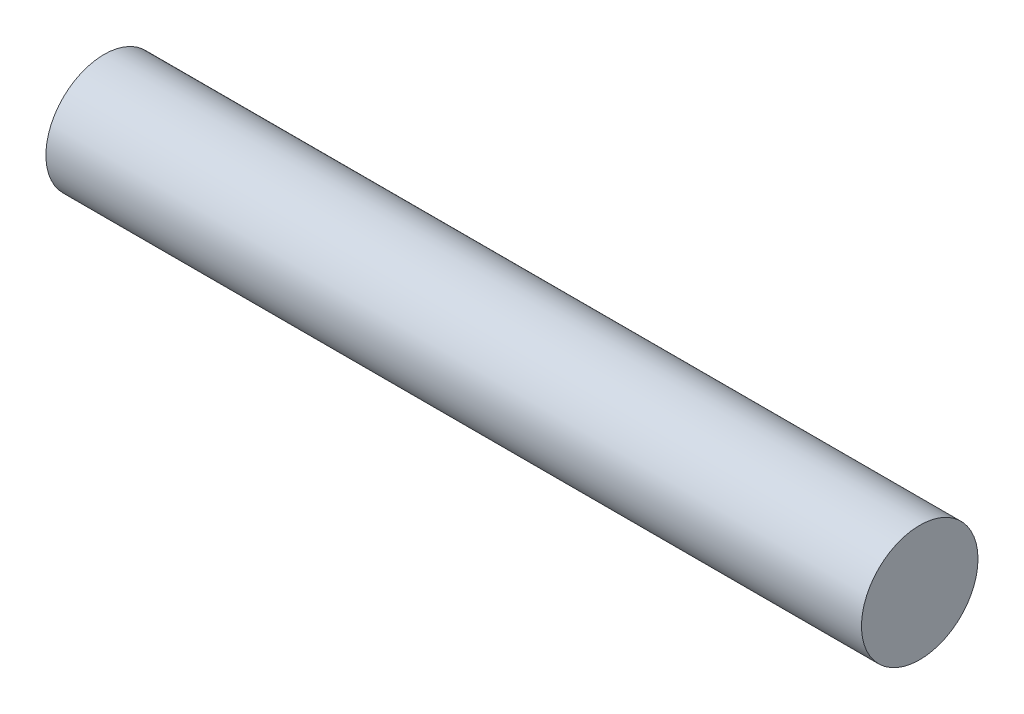
SolidWorks part; units mm, degrees
ref_plane "Ebene vorne" through (0, 0, 0) normal (0, 0, 1) x (1, 0, 0)
ref_plane "Ebene oben" through (0, 0, 0) normal (0, 1, 0) x (1, 0, 0)
ref_plane "Ebene rechts" through (0, 0, 0) normal (1, 0, 0) x (0, 0, -1)
sketch "Skizze1" plane through (0, 0, 0) normal (1, 0, 0) x (0, 0, -1)
  circle A0 centre (0, 0) radius 1
  dimension "D3" = 2
extrude "Linear austragen1" add sketch "Skizze1" along normal mid plane 14
